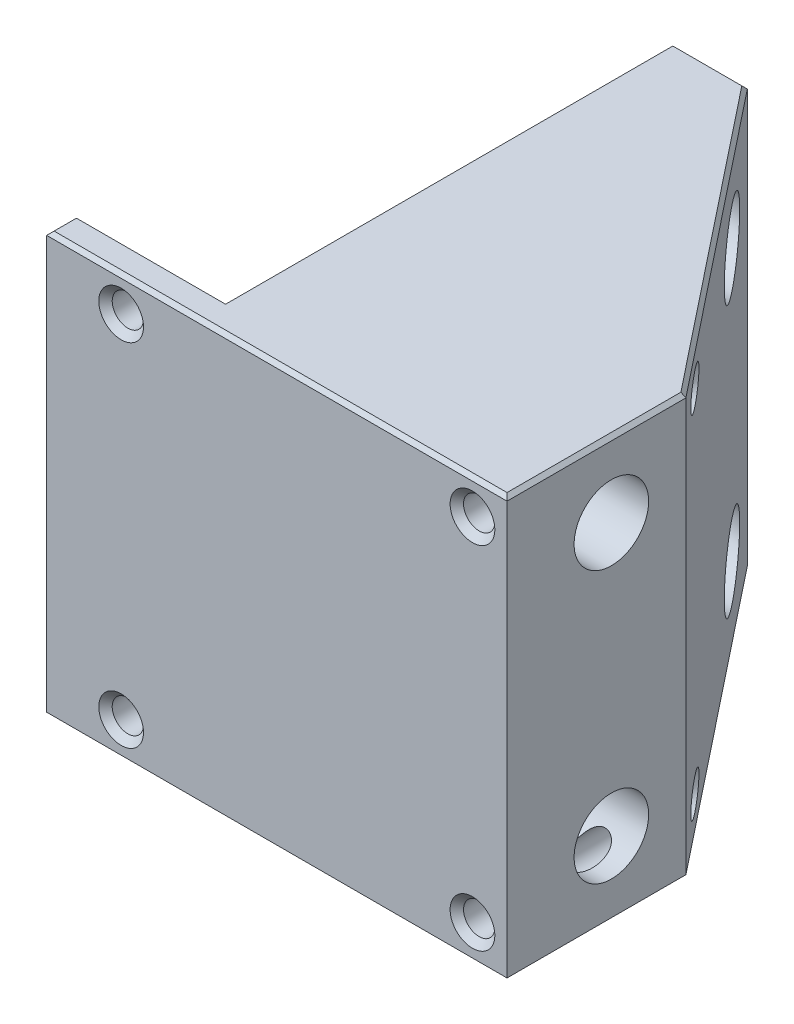
SolidWorks part; units mm, degrees
ref_plane "Front Plane" through (0, 0, 0) normal (0, 0, 1) x (1, 0, 0)
ref_plane "Top Plane" through (0, 0, 0) normal (0, 1, 0) x (1, 0, 0)
ref_plane "Right Plane" through (0, 0, 0) normal (1, 0, 0) x (0, 0, -1)
sketch "Sketch1" plane through (0, 0, 0) normal (0, 0, 1) x (1, 0, 0)
  line L1 (-30.88, 28.2) -> (30.88, 28.2)
  line L2 (-30.88, 28.2) -> (-30.88, -28.2)
  line L3 (-30.88, -28.2) -> (30.88, -28.2)
  line L4 (30.88, 28.2) -> (30.88, -28.2)
  line L5 (-30.88, 28.2) -> (30.88, -28.2) construction
  line L6 (-30.88, -28.2) -> (30.88, 28.2) construction
  point P0 (0, 0)
  dimension "D1" = 56.4
  dimension "D2" = 61.76
extrude "Boss-Extrude1" add sketch "Sketch1" along normal blind 4
sketch "Sketch9" plane through (0, 0, 4) normal (0, 0, 1) x (1, 0, 0)
  line L0 (30.88, 0) -> (2.68, 0) construction
  line L1 (30.88, -28.2) -> (30.88, 28.2) construction
  line L2 (2.68, 0) -> (2.68, 28.2) construction
  line L3 (30.88, 28.2) -> (-30.88, 28.2) construction
  circle A0 centre (2.68, 0) radius 2.5
  dimension "D1" = 5
sketch "Sketch12" plane through (0, 0, 4) normal (0, 0, 1) x (1, 0, 0)
  line L1 (26.245, 23.565) -> (-20.885, 23.565)
  line L2 (26.245, 23.565) -> (26.245, -23.565)
  line L3 (26.245, -23.565) -> (-20.885, -23.565)
  line L4 (-20.885, 23.565) -> (-20.885, -23.565)
  line L5 (26.245, 23.565) -> (-20.885, -23.565) construction
  line L6 (26.245, -23.565) -> (-20.885, 23.565) construction
  point P0 (2.68, 0)
  point P6 (4.5801, 8.5883)
  point P7 (2.68, 0)
  point P9 (2.68, 0)
  dimension "D1" = 47.13
hole_wizard "M5x0.8 Tapped Hole1" positions "Sketch13" profile "Sketch15" tap size "M5x0.8" standard "ANSI Metric" end condition through all
sketch "Sketch13" plane through (0, 0, 4) normal (0, 0, 1) x (1, 0, 0)
  point P0 (26.245, 23.565)
  point P3 (26.245, -23.565)
  point P6 (-20.885, -23.565)
  point P9 (-20.885, 23.565)
sketch "Sketch15" plane through (26.245, 23.565, 4) normal (1, 0, 0) x (0, -1, 0)
  line L0 (0, 0) -> (0, 4)
  line L1 (0, 4) -> (2.1, 4)
  line L2 (2.1, 4) -> (2.1, 0.9)
  line L3 (2.1, 0.9) -> (3, 0)
  line L5 (3, 0) -> (0, 0)
  line L6 (-2.1, 0.9) -> (-3, 0) construction
  line L11 (0, -6.35) -> (0, 107.95) construction
  dimension "Thru Tap Drill Dia." = 4.2
  dimension "Thru Tap Drill Depth" = 4
  dimension "Near C'Sink Dia." = 6
  dimension "Near C'Sink Angle" = 90
cosmetic thread "Hole Thread1" parameters "D2"=5
cosmetic thread "Hole Thread2" parameters "D2"=5
cosmetic thread "Hole Thread3" parameters "D2"=5
cosmetic thread "Hole Thread4" parameters "D2"=5
sketch "Sketch37" plane through (0, 0, 0) normal (0, 0, -1) x (-1, 0, 0)
  line L0 (-30.88, 28.2) -> (30.88, 28.2) construction
  line L1 (-30.88, -28.2) -> (10.88, -28.2)
  line L2 (-30.88, -28.2) -> (-30.88, 28.2)
  line L3 (-30.88, 28.2) -> (10.88, 28.2)
  line L4 (10.88, -28.2) -> (10.88, 28.2)
  line L5 (30.88, 28.2) -> (30.88, -28.2) construction
  circle A0 centre (-26.245, 23.565) radius 2.1 construction
  circle A1 centre (-26.245, -23.565) radius 2.1 construction
  circle A2 centre (-26.245, 23.565) radius 2.1
  circle A3 centre (-26.245, -23.565) radius 2.1
  dimension "D1" = 20
extrude "Boss-Extrude7" add sketch "Sketch37" along normal blind 60
sketch "Sketch40" plane through (0, -28.2, 0) normal (0, -1, 0) x (1, 0, 0)
  line L0 (-0.88, -60) -> (30.88, -20)
  line L1 (30.88, -60) -> (-10.88, -60) construction
  line L2 (30.88, 4) -> (30.88, -60) construction
  line L3 (30.88, -20) -> (30.88, -60)
  line L4 (30.88, -60) -> (-0.88, -60)
  line L5 (-30.88, 0) -> (-10.88, 0) construction
  line L6 (-10.88, -60) -> (-10.88, 0) construction
  dimension "D1" = 20
  dimension "D2" = 10
extrude "Cut-Extrude2" cut sketch "Sketch40" against normal through all
sketch "Sketch41" plane through (30.88, 0, 0) normal (1, 0, 0) x (0, 0, -1)
  line L0 (60, 28.2) -> (60, -28.2) construction
  line L1 (10, -18.2) -> (50, -18.2)
  line L2 (10, -18.2) -> (10, 18.2)
  line L3 (10, 18.2) -> (50, 18.2)
  line L4 (50, -18.2) -> (50, 18.2)
  line L6 (-4, -28.2) -> (20, -28.2) construction
  line L7 (-4, 28.2) -> (20, 28.2) construction
  line L8 (0, -28.2) -> (0, 28.2) construction
  dimension "D1" = 10
  dimension "D2" = 10
  dimension "D3" = 10
  dimension "D4" = 10
hole_wizard "CBORE for M5 SHCS3" positions "Sketch42" profile "Sketch44" counterbore size "M5" standard "ANSI Metric" end condition through all
sketch "Sketch42" plane through (30.88, 0, 0) normal (1, 0, 0) x (0, 0, -1)
  point P0 (10, -18.2)
  point P3 (10, 18.2)
  point P6 (50, 18.2)
  point P9 (50, -18.2)
sketch "Sketch44" plane through (30.88, -18.2, -10) normal (0, 1, 0) x (0, 0, -1)
  line L0 (0, 0) -> (0, 61.76)
  line L1 (0, 61.76) -> (2.75, 61.76)
  line L3 (2.75, 61.76) -> (2.75, 36.7)
  line L4 (2.75, 36.7) -> (5, 36.7)
  line L5 (5, 36.7) -> (5, 0)
  line L7 (5, 0) -> (0, 0)
  line L11 (0, -6.35) -> (0, 107.95) construction
  dimension "Thru Hole Dia." = 5.5
  dimension "Thru Hole Depth" = 61.76
  dimension "C'Bore Dia." = 10
  dimension "C'Bore Depth" = 36.7
chamfer "Chamfer7" distance 0.5 angle 45 14 edges at (0, 28.2, 4) (-30.88, 28.2, 2) (-20.88, 28.2, 0) (-10.88, 28.2, -30) (-5.88, 28.2, -60) (15, 28.2, -40) (30.88, 28.2, -8) (-10.88, -28.2, -30) (-20.88, -28.2, 0) (-30.88, -28.2, 2) (0, -28.2, 4) (30.88, -28.2, -8) (15, -28.2, -40) (-5.88, -28.2, -60)
